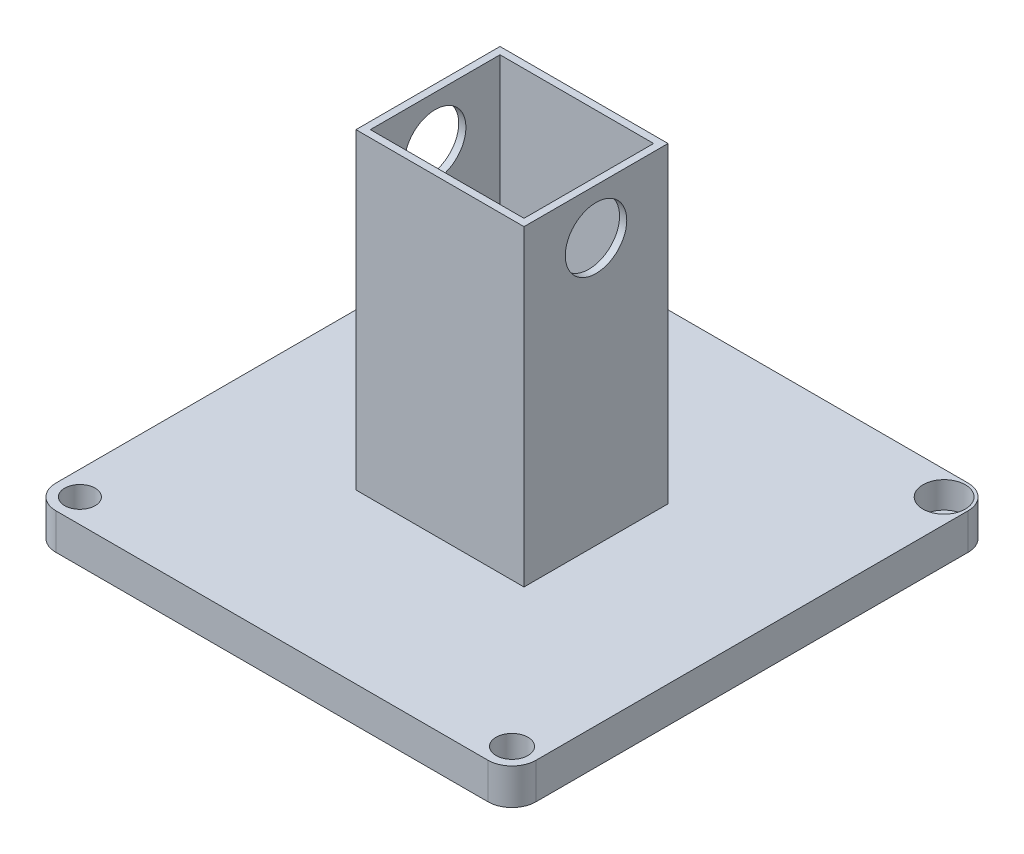
SolidWorks part; units mm, degrees
ref_plane "Alzado" through (0, 0, 0) normal (0, 0, 1) x (1, 0, 0)
ref_plane "Planta" through (0, 0, 0) normal (0, 1, 0) x (1, 0, 0)
ref_plane "Vista lateral" through (0, 0, 0) normal (1, 0, 0) x (0, 0, -1)
sketch "Croquis1" plane through (0, 0, 0) normal (0, 1, 0) x (1, 0, 0)
  line L1 (-90, 100) -> (90, 100)
  line L2 (-100, 90) -> (-100, -90)
  line L3 (-90, -100) -> (90, -100)
  line L4 (100, 90) -> (100, -90)
  line L5 (-100, 100) -> (100, -100) construction
  line L6 (-100, -100) -> (100, 100) construction
  arc A0 (90, 100) -> (100, 90) centre (90, 90) cw
  arc A1 (90, -100) -> (100, -90) centre (90, -90) ccw
  arc A2 (-100, -90) -> (-90, -100) centre (-90, -90) ccw
  arc A3 (-90, 100) -> (-100, 90) centre (-90, 90) ccw
  point P0 (0, 0)
  dimension "D3" = 10
  dimension "D1" = 200
  dimension "D2" = 200
extrude "Saliente-Extruir1" add sketch "Croquis1" along normal blind 15
sketch "Croquis2" plane through (0, 15, 0) normal (0, 1, 0) x (1, 0, 0)
  line L0 (-32, 27) -> (-32, -27)
  line L1 (-35, 30) -> (35, 30)
  line L2 (-35, 30) -> (-35, -30)
  line L3 (-35, -30) -> (35, -30)
  line L4 (35, 30) -> (35, -30)
  line L5 (-35, 30) -> (35, -30) construction
  line L6 (-35, -30) -> (35, 30) construction
  line L7 (-32, -27) -> (32, -27)
  line L8 (32, 27) -> (32, -27)
  line L9 (-32, 27) -> (32, 27)
  point P0 (0, 0)
  dimension "D1" = 70
  dimension "D2" = 60
  dimension "D3" = 3
extrude "Saliente-Extruir2" add sketch "Croquis2" along normal blind 130
sketch "Croquis3" plane through (35, 0, 0) normal (1, 0, 0) x (0, 0, -1)
  circle A0 centre (0, 125.915) radius 12.8049
extrude "Cortar-Extruir1" cut sketch "Croquis3" against normal blind 88
sketch "Croquis4" plane through (0, 15, 0) normal (0, 1, 0) x (1, 0, 0)
  circle A0 centre (-90, 90) radius 8.19
  circle A1 centre (90, 90) radius 8.8136
  circle A2 centre (-90, -90) radius 6.3403
  circle A3 centre (90, -90) radius 6.6334
extrude "Cortar-Extruir2" cut sketch "Croquis4" against normal blind 11
